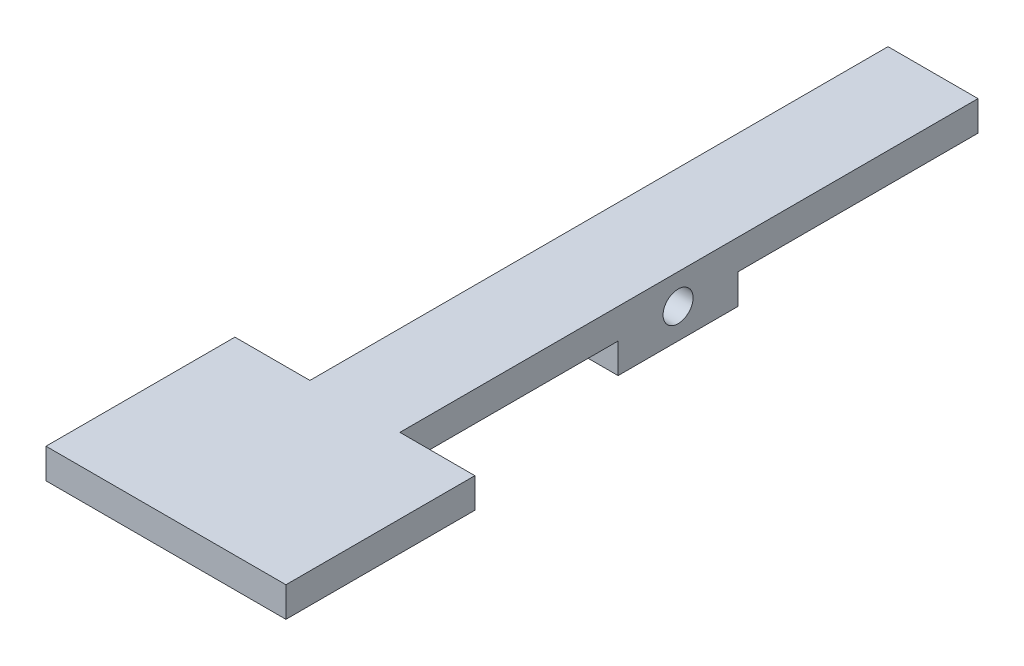
SolidWorks part; units mm, degrees
material "6061 Alloy"
ref_plane "Front Plane" through (0, 0, 0) normal (0, 0, 1) x (1, 0, 0)
ref_plane "Top Plane" through (0, 0, 0) normal (0, 1, 0) x (1, 0, 0)
ref_plane "Right Plane" through (0, 0, 0) normal (1, 0, 0) x (0, 0, -1)
sketch "Sketch1" plane through (0, 0, 0) normal (1, 0, 0) x (0, 0, -1)
  line L0 (0, 1.5875) -> (0, -1.5875)
  line L1 (0, -1.5875) -> (-25.4, -1.5875)
  line L5 (-76.2, 1.5875) -> (0, 1.5875)
  line L6 (-38.1, -1.5875) -> (-76.2, -1.5875)
  line L8 (-38.1, -1.5875) -> (-38.1, -4.7625)
  line L9 (-38.1, -4.7625) -> (-25.4, -4.7625)
  line L10 (-25.4, -1.5875) -> (-25.4, -4.7625)
  line L11 (-76.2, 1.5875) -> (-76.2, -1.5875)
  circle A0 centre (-31.75, -1.5875) radius 1.5875
  point P14 (-31.75, -4.7625)
  dimension "D6" = 3.175
  dimension "D1" = 3.175
  dimension "D4" = 76.2
  dimension "D5" = 3.175
  dimension "D7" = 12.7
  dimension "D8" = 38.1
extrude "Boss-Extrude1" add sketch "Sketch1" along normal blind 9.525
ref_plane "Center Plane" through (4.7625, 0, 0) normal (1, 0, 0) x (0, 0, -1)
sketch "Sketch3" plane through (4.7625, 0, 0) normal (1, 0, 0) x (0, 0, -1)
  line L2 (-76.2, -1.5875) -> (-61.2, -1.5875)
  line L4 (-61.2, -1.5875) -> (-61.2, 1.5875)
  line L5 (-76.2, 1.5875) -> (0, 1.5875) construction
  line L6 (-61.2, 1.5875) -> (-76.2, 1.5875)
  line L7 (-76.2, 1.5875) -> (-76.2, -1.5875)
  line L9 (-76.2, 1.5875) -> (-81.2, 1.5875)
  line L10 (-76.2, 1.5875) -> (-76.2, -1.5875)
  line L11 (-76.2, -1.5875) -> (-81.2, -1.5875)
  line L12 (-81.2, 1.5875) -> (-81.2, -1.5875)
  line L13 (-76.2, 1.5875) -> (-76.2, -1.5875) construction
  line L14 (-38.1, -1.5875) -> (-76.2, -1.5875) construction
  point P3 (-61.2, -4.7625)
  dimension "D1" = 15
  dimension "D2" = 20
extrude "Boss-Extrude2" add sketch "Sketch3" along normal mid plane 25.4 contours L6 L7 L2 L4 | L9 L12 L11 L7
